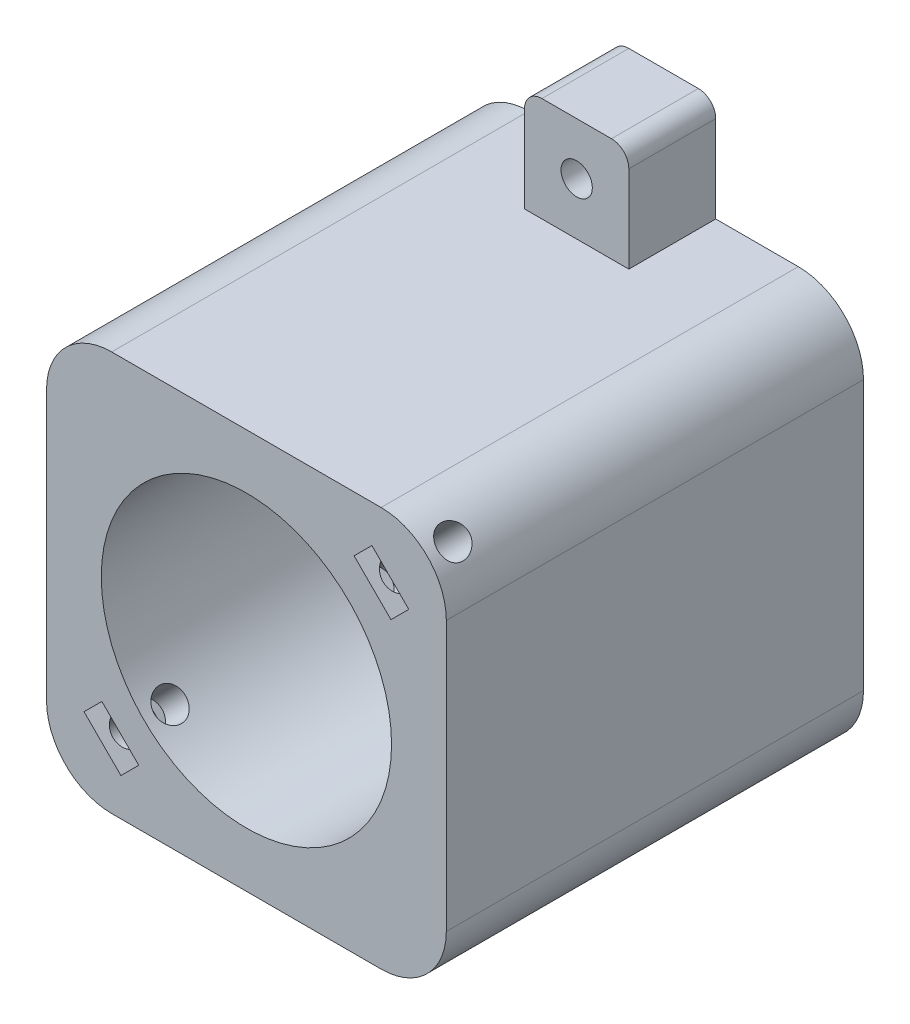
SolidWorks part; units mm, degrees
ref_plane "Plano frontal" through (0, 0, 0) normal (0, 0, 1) x (1, 0, 0)
ref_plane "Plano superior" through (0, 0, 0) normal (0, 1, 0) x (1, 0, 0)
ref_plane "Plano direito" through (0, 0, 0) normal (1, 0, 0) x (0, 0, -1)
other "Saida da Correia"
other "Test"
sketch "Sketch1" plane through (0, 0, 0) normal (0, 0, 1) x (1, 0, 0)
  line L1 (-15.5, 23) -> (15.5, 23)
  line L2 (-23, 15.5) -> (-23, -15.5)
  line L3 (-15.5, -23) -> (15.5, -23)
  line L4 (23, 15.5) -> (23, -15.5)
  line L5 (-23, 23) -> (23, -23) construction
  line L6 (-23, -23) -> (23, 23) construction
  arc A0 (15.5, -23) -> (23, -15.5) centre (15.5, -15.5) ccw
  arc A1 (15.5, 23) -> (23, 15.5) centre (15.5, 15.5) cw
  arc A2 (-15.5, 23) -> (-23, 15.5) centre (-15.5, 15.5) ccw
  arc A3 (-23, -15.5) -> (-15.5, -23) centre (-15.5, -15.5) ccw
  point P0 (0, 0)
  dimension "D3" = 7.5
  dimension "D1" = 46
  dimension "D2" = 46
extrude "Main" add sketch "Sketch1" along normal blind 48
sketch "Sketch2" plane through (0, 0, 0) normal (0, 0, -1) x (-1, 0, 0)
  circle A0 centre (0, 0) radius 16.7
  dimension "D1" = 33.4
extrude "Motor Hole" cut sketch "Sketch2" against normal through all
sketch "Sketch3" plane through (-23, 0, 0) normal (-1, 0, 0) x (0, 0, 1)
  line L0 (0, 15.5) -> (0, -15.5) construction
  line L1 (7, 15) -> (17, 15)
  line L2 (7, 15) -> (7, -15)
  line L3 (7, -15) -> (17, -15)
  line L4 (17, 15) -> (17, -15)
  line L5 (7, 15) -> (17, -15) construction
  line L6 (7, -15) -> (17, 15) construction
  line L8 (48, 15.5) -> (0, 15.5) construction
  point P0 (12, 0)
  dimension "D1" = 7
  dimension "D2" = 30
  dimension "D3" = 10
  dimension "D4" = 0.5
extrude "Pulley Out" cut sketch "Sketch3" against normal up to next
sketch "Sketch9" plane through (0, 0, 48) normal (0, 0, 1) x (1, 0, 0)
  line L0 (-20.8033, -20.8033) -> (20.8033, 20.8033) construction
  line L1 (-20.8033, 20.8033) -> (20.8033, -20.8033) construction
  line L2 (-18.682, -14.4393) -> (-16.6314, -12.3887)
  line L3 (-18.682, -14.4393) -> (-14.4393, -18.682)
  line L4 (-14.4393, -18.682) -> (-12.3887, -16.6314)
  line L5 (-16.6314, -12.3887) -> (-12.3887, -16.6314)
  line L6 (-18.682, -14.4393) -> (-12.3887, -16.6314) construction
  line L7 (-14.4393, -18.682) -> (-16.6314, -12.3887) construction
  line L8 (18.682, 14.4393) -> (16.6314, 12.3887)
  line L9 (12.3887, 16.6314) -> (16.6314, 12.3887)
  line L10 (18.682, 14.4393) -> (12.3887, 16.6314) construction
  line L11 (14.4393, 18.682) -> (16.6314, 12.3887) construction
  line L12 (14.4393, 18.682) -> (18.682, 14.4393)
  line L13 (14.4393, 18.682) -> (12.3887, 16.6314)
  arc A0 (-23, -15.5) -> (-15.5, -23) centre (-15.5, -15.5) ccw construction
  arc A1 (23, 15.5) -> (15.5, 23) centre (15.5, 15.5) ccw construction
  arc A2 (-15.5, 23) -> (-23, 15.5) centre (-15.5, 15.5) ccw construction
  arc A3 (15.5, -23) -> (23, -15.5) centre (15.5, -15.5) ccw construction
  point P8 (-15.5354, -15.5354)
  dimension "D1" = 6
  dimension "D2" = 2.9
  dimension "D3" = 6
extrude "Nuts" cut sketch "Sketch9" against normal blind 6
sketch3d "3DSketch4"
  line L0 (-20.8033, -20.8033, 48) -> (-20.8033, -20.8033, 0) construction
  arc A0 (-23, -15.5, 48) -> (-15.5, -23, 48) centre (-15.5, -15.5, 48) ccw construction
  arc A1 (-23, -15.5, 0) -> (-15.5, -23, 0) centre (-15.5, -15.5, 0) ccw construction
  point P5 (-15.5, -15.5, 55.5)
  point P9 (-15.5, -15.5, 7.5)
  point P10 (-20.8033, -20.8033, 45)
  dimension "D1" = 3
hole_wizard "M3 Clearance Hole1" positions "3DSketch7" profile "Sketch13" hole size "M3" standard "ANSI Metric"
sketch3d "3DSketch7"
  point P0 (-20.8033, -20.8033, 45)
  point P2 (-30.805, -61.7642, 0)
sketch "Sketch13" plane through (-20.8033, -20.8033, 45) normal (0, 0, 1) x (0.7071, -0.7071, 0)
  line L0 (0, 0) -> (0, 61.9472)
  line L1 (0, 61.9472) -> (1.8, 61.9472)
  line L2 (1.8, 61.9472) -> (1.8, 0)
  line L5 (1.8, 0) -> (0, 0)
  line L11 (0, -6.35) -> (0, 107.95) construction
  dimension "Thru Hole Dia." = 3.6
  dimension "Thru Hole Depth" = 61.9472
sketch "Sketch15" plane through (0, 0, 0) normal (0, 0, -1) x (-1, 0, 0)
  line L0 (-6, -23) -> (6, -23)
  line L1 (-6, -23) -> (-6, -33)
  line L2 (6, -23) -> (6, -33)
  line L3 (-4, -35) -> (4, -35)
  line L4 (15.5, -23) -> (-15.5, -23) construction
  line L5 (-6, -23.1196) -> (6, -23.1196) construction
  line L6 (-23, 0) -> (23, 0) construction
  line L7 (-23, -15.5) -> (-23, 15.5) construction
  line L8 (23, 15.5) -> (23, -15.5) construction
  line L9 (-4, 35) -> (4, 35)
  line L10 (6, 23) -> (6, 33)
  line L11 (-6, 23) -> (6, 23)
  line L12 (-6, 23) -> (-6, 33)
  arc A0 (6, -33) -> (4, -35) centre (4, -33) cw
  arc A1 (-6, -33) -> (-4, -35) centre (-4, -33) ccw
  arc A2 (-6, 33) -> (-4, 35) centre (-4, 33) cw
  arc A3 (6, 33) -> (4, 35) centre (4, 33) ccw
  point P8 (0, -23.1196)
  point P9 (0, -23)
  point P12 (6, -35)
  point P15 (-6, -35)
  dimension "D4" = 2
  dimension "D1" = 12
  dimension "D2" = 12
  dimension "D3" = 0
extrude "Boss-Extrude2" add sketch "Sketch15" against normal blind 10
hole_wizard "M3 Clearance Hole2" positions "Sketch17" profile "Sketch16" hole size "M3" standard "ANSI Metric" end condition through all
sketch "Sketch17" plane through (0, 0, 0) normal (0, 0, -1) x (-1, 0, 0)
  line L0 (5.4142, 34.4142) -> (-6, 23) construction
  line L2 (-5.4142, 34.4142) -> (6, 23) construction
  line L3 (5.4142, -34.4142) -> (-6, -23)
  line L5 (-5.4142, -34.4142) -> (6, -23) construction
  arc A0 (6, 33) -> (4, 35) centre (4, 33) ccw construction
  arc A2 (-4, 35) -> (-6, 33) centre (-4, 33) ccw construction
  arc A3 (4, -35) -> (6, -33) centre (4, -33) ccw construction
  arc A4 (-6, -33) -> (-4, -35) centre (-4, -33) ccw construction
  point P0 (0, -29)
  point P2 (0, 29)
  point P23 (0, 29)
sketch "Sketch16" plane through (0, -29, 0) normal (1, 0, 0) x (0, 1, 0)
  line L0 (0, 0) -> (0, 48)
  line L1 (0, 48) -> (1.8, 48)
  line L2 (1.8, 48) -> (1.8, 0)
  line L5 (1.8, 0) -> (0, 0)
  line L11 (0, -6.35) -> (0, 107.95) construction
  dimension "Thru Hole Dia." = 3.6
  dimension "Thru Hole Depth" = 48
